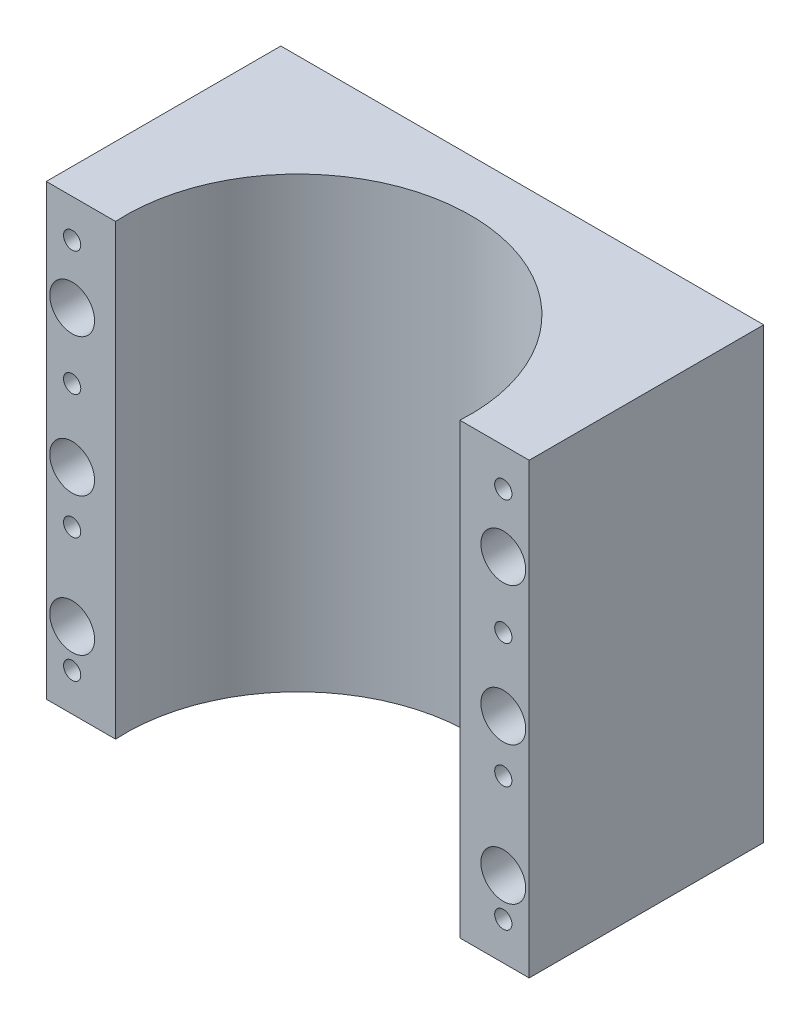
SolidWorks part; units mm, degrees
ref_plane "前视基准面" through (0, 0, 0) normal (0, 0, 1) x (1, 0, 0)
ref_plane "上视基准面" through (0, 0, 0) normal (0, 1, 0) x (1, 0, 0)
ref_plane "右视基准面" through (0, 0, 0) normal (1, 0, 0) x (0, 0, -1)
other "Configuration Table"
sketch "草图1" plane through (0, 0, 0) normal (0, 0, 1) x (1, 0, 0)
  line L1 (0, 0) -> (140, 0)
  line L2 (0, 0) -> (0, -130)
  line L3 (0, -130) -> (140, -130)
  line L4 (140, 0) -> (140, -130)
  dimension "D1" = 140
  dimension "D2" = 130
extrude "凸台-拉伸1" add sketch "草图1" along normal blind 68
sketch "草图2" plane through (0, 0, 0) normal (0, 1, 0) x (1, 0, 0)
  line L0 (70, 0) -> (70, -68) construction
  line L1 (140, 0) -> (0, 0) construction
  line L2 (140, -68) -> (0, -68) construction
  circle A0 centre (70, -65) radius 50
  dimension "D1" = 100
  dimension "D2" = 65
extrude "切除-拉伸2" cut sketch "草图2" against normal through all
sketch "草图3" plane through (0, 0, 68) normal (0, 0, 1) x (1, 0, 0)
  line L1 (0, 0) -> (0, -130) construction
  line L3 (20.0901, 0) -> (0, 0) construction
  circle A0 centre (7.5, -28) radius 6.5
  circle A1 centre (132.5, -28) radius 6.5
  circle A2 centre (132.5, -68) radius 6.5
  circle A3 centre (132.5, -108) radius 6.5
  circle A4 centre (7.5, -68) radius 6.5
  circle A5 centre (7.5, -108) radius 6.5
  dimension "D2" = 13
  dimension "D1" = 7.5
  dimension "D3" = 28
  dimension "D4" = 2
  dimension "D5" = 3
extrude "切除-拉伸3" cut sketch "草图3" against normal blind 35
sketch "草图4" plane through (0, 0, 33) normal (0, 0, 1) x (1, 0, 0)
  circle A1 centre (132.5, -28) radius 4
  circle A2 centre (7.5, -28) radius 4
  circle A3 centre (7.5, -28) radius 4
  circle A4 centre (132.5, -68) radius 4
  circle A5 centre (132.5, -108) radius 4
  circle A6 centre (7.5, -68) radius 4
  circle A7 centre (7.5, -108) radius 4
  dimension "D2" = 2
  dimension "D1" = 2.5
  dimension "D3" = 3
extrude "切除-拉伸4" cut sketch "草图4" against normal through all
hole_wizard "M6 螺纹孔10" positions "草图9" profile "草图10" tap size "M6" standard "GB"
sketch "草图9" plane through (0, 0, 68) normal (0, 0, 1) x (1, 0, 0)
  point P0 (7.5, -11)
  point P3 (7.5, -47)
  point P6 (7.5, -83)
  point P15 (132.5, -83)
  point P18 (132.5, -47)
  point P21 (132.5, -11)
  point P29 (7.5, -119)
  point P32 (132.5, -119)
sketch "草图10" plane through (7.5, -11, 68) normal (1, 0, 0) x (0, -1, 0)
  line L0 (0, 0) -> (0, 16.5022)
  line L1 (0, 16.5022) -> (2.5, 15)
  line L2 (2.5, 15) -> (2.5, 0)
  line L5 (2.5, 0) -> (0, 0)
  line L10 (0, 16.5022) -> (-2.5, 15) construction
  line L11 (0, -6.35) -> (0, 107.95) construction
  dimension "螺纹孔钻头直径" = 5
  dimension "螺纹孔钻头深度" = 15
  dimension "导头角度" = 118
cosmetic thread "孔螺蚊线9" parameters "D1"=12, "D2"=6
cosmetic thread "孔螺蚊线10" parameters "D1"=12, "D2"=6
cosmetic thread "孔螺蚊线11" parameters "D1"=12, "D2"=6
cosmetic thread "孔螺蚊线12" parameters "D1"=12, "D2"=6
cosmetic thread "孔螺蚊线13" parameters "D1"=12, "D2"=6
cosmetic thread "孔螺蚊线14" parameters "D1"=12, "D2"=6
cosmetic thread "孔螺蚊线15" parameters "D1"=12, "D2"=6
cosmetic thread "孔螺蚊线16" parameters "D1"=12, "D2"=6
